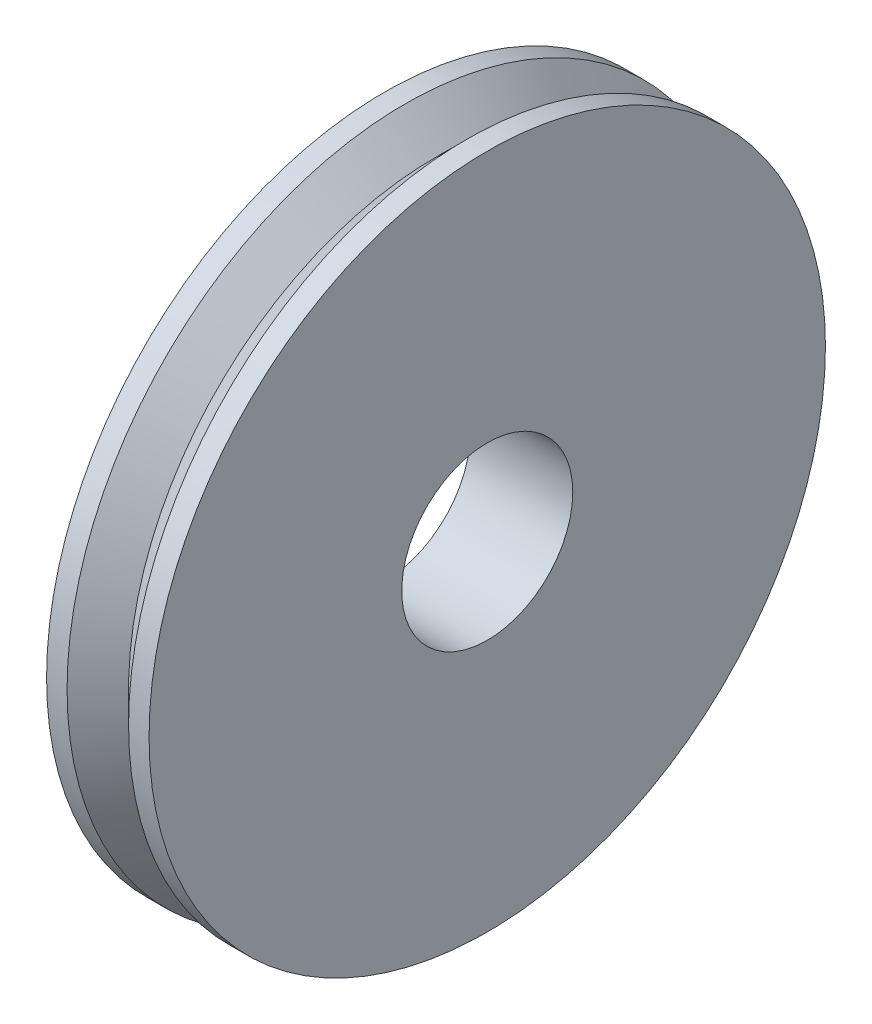
SolidWorks part; units mm, degrees
ref_plane "Front Plane" through (0, 0, 0) normal (0, 0, 1) x (1, 0, 0)
ref_plane "Top Plane" through (0, 0, 0) normal (0, 1, 0) x (1, 0, 0)
ref_plane "Right Plane" through (0, 0, 0) normal (1, 0, 0) x (0, 0, -1)
ref_plane "Plane1" through (32.0157, 0, 0) normal (1, 0, 0) x (0, 0, -1)
ref_point "Point1"
ref_point "Point2"
sketch "Sketch1" plane through (32.0157, 0, 0) normal (1, 0, 0) x (0, 0, -1)
  line L0 (-54.1719, 76.1362) -> (-54.1719, 61.6362) construction
  line L2 (-54.1719, 68.8862) -> (136.3281, 68.8862) construction
  circle A0 centre (136.3281, 49.8362) radius 19.05
  dimension "D1" = 38.1
  dimension "D2" = 190.5
extrude "Boss-Extrude1" add sketch "Sketch1" along normal mid plane 3.81
ref_plane "Plane2" through (0, 0, -155.3781) normal (0, 0, -1) x (-1, 0, 0)
ref_plane "Plane3" through (0, 0, -136.3281) normal (0, 0, -1) x (-1, 0, 0)
sketch "Sketch5" plane through (0, 0, -136.3281) normal (0, 0, -1) x (-1, 0, 0)
  line L0 (-32.0157, 68.8862) -> (-33.9207, 70.7912)
  line L5 (-30.1107, 68.8862) -> (-33.9207, 68.8862) construction
  line L6 (-30.1107, 68.8862) -> (-33.9207, 68.8862) construction
  line L7 (-33.9207, 70.7912) -> (-35.1907, 70.7912)
  line L8 (-35.1907, 70.7912) -> (-35.1907, 49.8362)
  line L9 (-35.1907, 49.8362) -> (-33.9207, 49.8362)
  line L10 (-33.9207, 68.8862) -> (-33.9207, 30.7862) construction
  line L11 (-33.9207, 49.8362) -> (-33.9207, 68.8862)
  line L12 (-33.9207, 68.8862) -> (-32.0157, 68.8862)
  point P7 (-34.5557, 70.7912)
  point P8 (-36.5928, 70.7912)
  point P9 (0, 0)
  dimension "D1" = 1.905
  dimension "D2" = 1.27
ref_axis "Axis1" through (33.9207, 49.8362, -136.3281) along (-1, 0, 0)
revolve "Revolve1" add sketch "Sketch5" angle 360 about axis through (33.9207, 49.8362, -136.3281) along (-1, 0, 0)
mirror "Mirror2" about plane through (32.0157, 0, 0) normal (1, 0, 0) of "Revolve1"
sketch "Sketch6" plane through (35.1907, 0, 0) normal (1, 0, 0) x (0, 0, -1)
  circle A0 centre (136.3281, 49.8362) radius 5.3
  dimension "D1" = 10.6
extrude "Cut-Extrude2" cut sketch "Sketch6" against normal through all
